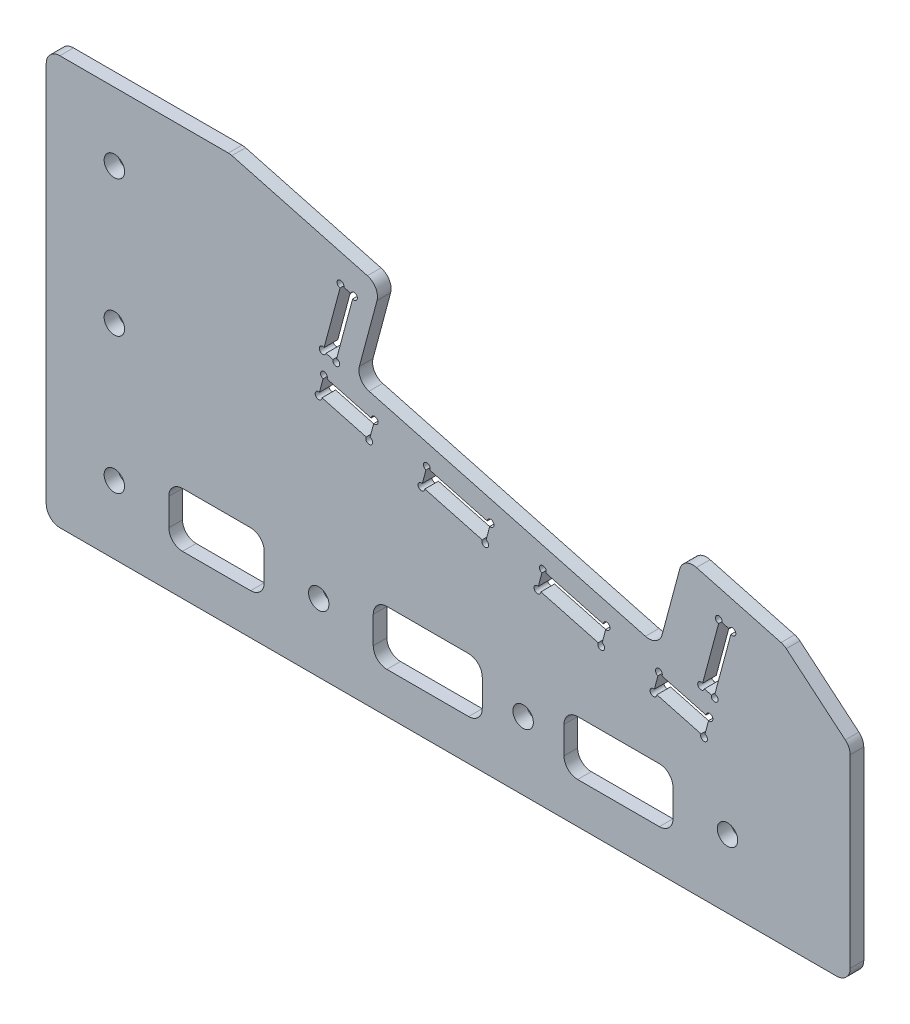
SolidWorks part; units mm, degrees
material "Thornel Mat VMA"
ref_plane "前视基准面" through (0, 0, 0) normal (0, 0, 1) x (1, 0, 0)
ref_plane "上视基准面" through (0, 0, 0) normal (0, 1, 0) x (1, 0, 0)
ref_plane "右视基准面" through (0, 0, 0) normal (1, 0, 0) x (0, 0, -1)
sketch "草图1" plane through (0, 0, 0) normal (0, 0, 1) x (1, 0, 0)
  line L1 (0, 0) -> (130, 0)
  line L2 (0, 0) -> (0, 60)
  line L3 (0, 60) -> (130, 60)
  line L4 (130, 0) -> (130, 60)
  circle A0 centre (10, 10) radius 1.5
  circle A1 centre (10, 30) radius 1.5
  circle A2 centre (10, 50) radius 1.5
  circle A3 centre (40, 10) radius 1.5
  circle A4 centre (70, 10) radius 1.5
  circle A5 centre (100, 10) radius 1.5
  dimension "D3" = 3
  dimension "D1" = 60
  dimension "D2" = 130
  dimension "D4" = 10
  dimension "D5" = 10
  dimension "D6" = 20
  dimension "D7" = 20
  dimension "D8" = 30
  dimension "D9" = 30
  dimension "D10" = 30
extrude "凸台-拉伸1" add sketch "草图1" along normal blind 2
sketch "草图2" plane through (0, 0, 2) normal (0, 0, 1) x (1, 0, 0)
  line L0 (27, 60) -> (130, 32.4012)
  line L1 (130, 60) -> (0, 60) construction
  line L2 (130, 0) -> (130, 60) construction
  line L3 (0, 60) -> (0, 0) construction
  line L4 (27, 60) -> (130, 60)
  line L5 (130, 60) -> (130, 32.4012)
  dimension "D1" = 27
  dimension "D2" = 15
extrude "切除-拉伸1" cut sketch "草图2" against normal through all
sketch "草图3" plane through (0, 0, 2) normal (0, 0, 1) x (1, 0, 0)
  line L0 (49.0714, 54.086) -> (93.504, 42.1803)
  line L1 (49.0714, 54.086) -> (45.4479, 40.563)
  line L2 (93.504, 42.1803) -> (89.8805, 28.6573)
  line L3 (45.4479, 40.563) -> (89.8805, 28.6573)
  line L4 (27, 60) -> (130, 32.4012) construction
  dimension "D1" = 14
  dimension "D2" = 46
  dimension "D3" = 22.85
extrude "切除-拉伸2" cut sketch "草图3" against normal through all
sketch "草图4" plane through (0, 0, 2) normal (0, 0, 1) x (1, 0, 0)
  line L0 (45.4479, 40.563) -> (89.8805, 28.6573) construction
  line L1 (98.7472, 36.6343) -> (96.159, 26.975)
  line L2 (96.159, 26.975) -> (98.0909, 26.4574)
  line L3 (98.0909, 26.4574) -> (100.6791, 36.1166)
  line L4 (49.0714, 54.086) -> (45.4479, 40.563) construction
  line L5 (100.6791, 36.1166) -> (98.7472, 36.6343)
  line L7 (89.8805, 28.6573) -> (93.504, 42.1803) construction
  line L8 (45.1384, 50.9987) -> (42.5502, 41.3395)
  line L9 (45.1384, 50.9987) -> (43.2065, 51.5164)
  line L10 (42.5502, 41.3395) -> (40.6183, 41.8571)
  line L11 (43.2065, 51.5164) -> (40.6183, 41.8571)
  line L13 (93.504, 42.1803) -> (130, 32.4012) construction
  dimension "D2" = 3
  dimension "D3" = 6.5
  dimension "D4" = 4
  dimension "D5" = 10
  dimension "D6" = 2
  dimension "D18" = 10
  dimension "D19" = 2
extrude "切除-拉伸5" cut sketch "草图4" against normal blind 10
sketch "草图5" plane through (0, 0, 2) normal (0, 0, 1) x (1, 0, 0)
  line L0 (108.2873, 38.2191) -> (130, 20) construction
  line L1 (93.504, 42.1803) -> (130, 32.4012) construction
  line L2 (130, 0) -> (130, 32.4012) construction
  line L3 (130, 20) -> (130, 32.4012)
  line L4 (130, 32.4012) -> (108.2873, 38.2191)
  line L5 (130, 20) -> (0, 20) construction
  line L6 (0, 60) -> (0, 0) construction
  line L7 (20, 0) -> (180, 0) construction
  line L8 (118, 30.0692) -> (118, 0)
  line L9 (118, 0) -> (130, 0)
  line L10 (130, 0) -> (130, 20)
  line L11 (108.2873, 38.2191) -> (118, 30.0692)
  dimension "D1" = 20
  dimension "D2" = 40
  dimension "D3" = 12
extrude "切除-拉伸6" cut sketch "草图5" against normal through all
fillet "圆角1" radius 2 10 edges at (0, 0, 1) (27, 60, 1) (49.0714, 54.086, 1) (45.4479, 40.563, 1) (89.8805, 28.6573, 1) (93.504, 42.1803, 1) (0, 60, 1) (118, 0, 1) (118, 30.0692, 1) (108.2873, 38.2191, 1)
sketch "草图6" plane through (0, 0, 0) normal (0, 0, -1) x (-1, 0, 0)
  line L0 (-30, 6) -> (-20, 6) construction
  line L1 (-18, 8) -> (-18, 12) construction
  line L2 (-20, 14) -> (-30, 14) construction
  line L3 (-32, 12) -> (-32, 8) construction
  line L4 (-62, 6) -> (-50, 6) construction
  line L5 (-48, 8) -> (-48, 12) construction
  line L6 (-50, 14) -> (-62, 14) construction
  line L7 (-64, 12) -> (-64, 8) construction
  line L8 (-78, 14) -> (-90, 14) construction
  line L9 (-76, 8) -> (-76, 12) construction
  line L10 (-118, 29.1366) -> (-118, 2)
  line L11 (-116, 0) -> (-2, 0)
  line L12 (0, 2) -> (0, 58)
  line L13 (-2, 60) -> (-26.7367, 60)
  line L14 (-27.2543, 59.9319) -> (-47.1396, 54.6036)
  line L15 (-48.5538, 52.1541) -> (-45.9656, 42.4949)
  line L16 (-47.3798, 40.0454) -> (-87.9487, 29.175)
  line L17 (-90.3982, 30.5892) -> (-92.9864, 40.2485)
  line L18 (-95.4358, 41.6627) -> (-107.859, 38.3339)
  line L19 (-108.6269, 37.9341) -> (-117.2856, 30.6687)
  line L20 (-118, 29.1366) -> (-118, 2)
  line L21 (-116, 0) -> (-2, 0)
  line L22 (0, 2) -> (0, 58)
  line L23 (-2, 60) -> (-26.7367, 60)
  line L24 (-27.2543, 59.9319) -> (-47.1396, 54.6036)
  line L25 (-48.5538, 52.1541) -> (-45.9656, 42.4949)
  line L26 (-47.3798, 40.0454) -> (-87.9487, 29.175)
  line L27 (-90.3982, 30.5892) -> (-92.9864, 40.2485)
  line L28 (-95.4358, 41.6627) -> (-107.859, 38.3339)
  line L29 (-108.6269, 37.9341) -> (-117.2856, 30.6687)
  line L30 (-90, 6) -> (-78, 6) construction
  line L31 (-92, 12) -> (-92, 8) construction
  line L32 (-30, 6) -> (-20, 6)
  line L33 (-18, 8) -> (-18, 12)
  line L34 (-20, 14) -> (-30, 14)
  line L35 (-32, 12) -> (-32, 8)
  line L36 (-62, 6) -> (-50, 6)
  line L37 (-48, 8) -> (-48, 12)
  line L38 (-50, 14) -> (-62, 14)
  line L39 (-64, 12) -> (-64, 8)
  line L40 (-78, 14) -> (-90, 14)
  line L41 (-76, 8) -> (-76, 12)
  line L42 (-90, 6) -> (-78, 6)
  line L43 (-92, 12) -> (-92, 8)
  arc A0 (-124, 8) -> (-122, 6) centre (-122, 8) ccw construction
  arc A1 (-124, 8) -> (-122, 6) centre (-122, 8) ccw
  arc A2 (-32, 8) -> (-30, 6) centre (-30, 8) ccw construction
  arc A3 (-20, 6) -> (-18, 8) centre (-20, 8) ccw construction
  arc A4 (-18, 12) -> (-20, 14) centre (-20, 12) ccw construction
  arc A5 (-30, 14) -> (-32, 12) centre (-30, 12) ccw construction
  arc A6 (-64, 8) -> (-62, 6) centre (-62, 8) ccw construction
  arc A7 (-50, 6) -> (-48, 8) centre (-50, 8) ccw construction
  arc A8 (-48, 12) -> (-50, 14) centre (-50, 12) ccw construction
  arc A9 (-62, 14) -> (-64, 12) centre (-62, 12) ccw construction
  arc A10 (-118, 2) -> (-116, 0) centre (-116, 2) ccw
  arc A11 (-2, 0) -> (0, 2) centre (-2, 2) ccw
  arc A12 (0, 58) -> (-2, 60) centre (-2, 58) ccw
  arc A13 (-26.7367, 60) -> (-27.2543, 59.9319) centre (-26.7367, 58) ccw
  arc A14 (-47.1396, 54.6036) -> (-48.5538, 52.1541) centre (-46.6219, 52.6718) ccw
  arc A15 (-47.3798, 40.0454) -> (-45.9656, 42.4949) centre (-47.8974, 41.9772) ccw
  arc A16 (-90.3982, 30.5892) -> (-87.9487, 29.175) centre (-88.4663, 31.1068) ccw
  arc A17 (-92.9864, 40.2485) -> (-95.4358, 41.6627) centre (-94.9182, 39.7308) ccw
  arc A18 (-107.859, 38.3339) -> (-108.6269, 37.9341) centre (-107.3414, 36.402) ccw
  arc A19 (-117.2856, 30.6687) -> (-118, 29.1366) centre (-116, 29.1366) ccw
  arc A20 (-118, 2) -> (-116, 0) centre (-116, 2) ccw
  arc A21 (-2, 0) -> (0, 2) centre (-2, 2) ccw
  arc A22 (0, 58) -> (-2, 60) centre (-2, 58) ccw
  arc A23 (-26.7367, 60) -> (-27.2543, 59.9319) centre (-26.7367, 58) ccw
  arc A24 (-47.1396, 54.6036) -> (-48.5538, 52.1541) centre (-46.6219, 52.6718) ccw
  arc A25 (-47.3798, 40.0454) -> (-45.9656, 42.4949) centre (-47.8974, 41.9772) ccw
  arc A26 (-90.3982, 30.5892) -> (-87.9487, 29.175) centre (-88.4663, 31.1068) ccw
  arc A27 (-92.9864, 40.2485) -> (-95.4358, 41.6627) centre (-94.9182, 39.7308) ccw
  arc A28 (-107.859, 38.3339) -> (-108.6269, 37.9341) centre (-107.3414, 36.402) ccw
  arc A29 (-117.2856, 30.6687) -> (-118, 29.1366) centre (-116, 29.1366) ccw
  arc A30 (-76, 12) -> (-78, 14) centre (-78, 12) ccw construction
  arc A31 (-78, 6) -> (-76, 8) centre (-78, 8) ccw construction
  arc A32 (-92, 8) -> (-90, 6) centre (-90, 8) ccw construction
  arc A33 (-90, 14) -> (-92, 12) centre (-90, 12) ccw construction
  arc A34 (-32, 8) -> (-30, 6) centre (-30, 8) ccw
  arc A35 (-20, 6) -> (-18, 8) centre (-20, 8) ccw
  arc A36 (-18, 12) -> (-20, 14) centre (-20, 12) ccw
  arc A37 (-30, 14) -> (-32, 12) centre (-30, 12) ccw
  arc A38 (-64, 8) -> (-62, 6) centre (-62, 8) ccw
  arc A39 (-50, 6) -> (-48, 8) centre (-50, 8) ccw
  arc A40 (-48, 12) -> (-50, 14) centre (-50, 12) ccw
  arc A41 (-62, 14) -> (-64, 12) centre (-62, 12) ccw
  arc A42 (-76, 12) -> (-78, 14) centre (-78, 12) ccw
  arc A43 (-78, 6) -> (-76, 8) centre (-78, 8) ccw
  arc A44 (-92, 8) -> (-90, 6) centre (-90, 8) ccw
  arc A45 (-90, 14) -> (-92, 12) centre (-90, 12) ccw
  dimension "D1" = 0
extrude "切除-拉伸7" cut sketch "草图6" against normal blind 3 contours L40 A45 L43 A44 L42 A43 L41 A42 | L38 A41 L39 A38 L36 A39 L37 A40 | L34 A37 L35 A34 L32 A35 L33 A36
sketch "草图7" plane through (0, 0, 2) normal (0, 0, 1) x (1, 0, 0)
  line L0 (98.0909, 26.4574) -> (95.0706, 15.1855) construction
  line L1 (97.3144, 23.5596) -> (89.9444, 25.5344)
  line L2 (89.9444, 25.5344) -> (89.168, 22.6366)
  line L3 (89.168, 22.6366) -> (96.538, 20.6618)
  line L4 (96.538, 20.6618) -> (97.3144, 23.5596)
  line L5 (96.159, 26.975) -> (98.0909, 26.4574) construction
  line L6 (34.4437, 37.2999) -> (89.168, 22.6366) construction
  line L7 (81.4406, 24.7072) -> (82.217, 27.6049)
  line L8 (82.217, 27.6049) -> (72.9152, 30.0974)
  line L9 (72.9152, 30.0974) -> (72.1387, 27.1996)
  line L10 (72.1387, 27.1996) -> (81.4406, 24.7072)
  line L11 (64.4113, 29.2702) -> (65.1877, 32.1679)
  line L12 (65.1877, 32.1679) -> (55.8859, 34.6604)
  line L13 (55.8859, 34.6604) -> (55.1094, 31.7626)
  line L14 (55.1094, 31.7626) -> (64.4113, 29.2702)
  line L15 (47.382, 33.8331) -> (48.1585, 36.7309)
  line L16 (48.1585, 36.7309) -> (40.7885, 38.7057)
  line L17 (40.7885, 38.7057) -> (40.012, 35.8079)
  line L18 (40.012, 35.8079) -> (47.382, 33.8331)
  dimension "D4" = 7.63
  dimension "D1" = 3
  dimension "D2" = 3
  dimension "D3" = 7.63
  dimension "D5" = 9.63
  dimension "D6" = 9.63
  dimension "D7" = 8
  dimension "D8" = 8
  dimension "D9" = 8
extrude "切除-拉伸8" cut sketch "草图7" against normal blind 10
sketch "草图8" plane through (0, 0, 2) normal (0, 0, 1) x (1, 0, 0)
  line L0 (98.726, 36.671) -> (96.1223, 26.9538)
  line L1 (96.1223, 26.9538) -> (98.1121, 26.4206)
  line L2 (98.1121, 26.4206) -> (100.7158, 36.1379)
  line L3 (100.7158, 36.1379) -> (98.726, 36.671)
  line L4 (98.7472, 36.6343) -> (96.159, 26.975)
  line L5 (100.6791, 36.1166) -> (98.7472, 36.6343)
  line L6 (98.0909, 26.4574) -> (100.6791, 36.1166)
  line L7 (96.159, 26.975) -> (98.0909, 26.4574)
  line L8 (98.7472, 36.6343) -> (96.159, 26.975)
  line L9 (100.6791, 36.1166) -> (98.7472, 36.6343)
  line L10 (98.0909, 26.4574) -> (100.6791, 36.1166)
  line L11 (96.159, 26.975) -> (98.0909, 26.4574)
  line L12 (97.3144, 23.5596) -> (89.9444, 25.5344)
  line L13 (96.538, 20.6618) -> (97.3144, 23.5596)
  line L14 (89.168, 22.6366) -> (96.538, 20.6618)
  line L15 (89.9444, 25.5344) -> (89.168, 22.6366)
  line L16 (97.3144, 23.5596) -> (89.9444, 25.5344)
  line L17 (96.538, 20.6618) -> (97.3144, 23.5596)
  line L18 (89.168, 22.6366) -> (96.538, 20.6618)
  line L19 (89.9444, 25.5344) -> (89.168, 22.6366)
  line L20 (81.4406, 24.7072) -> (82.217, 27.6049)
  line L21 (72.1387, 27.1996) -> (81.4406, 24.7072)
  line L22 (72.9152, 30.0974) -> (72.1387, 27.1996)
  line L23 (82.217, 27.6049) -> (72.9152, 30.0974)
  line L24 (81.4406, 24.7072) -> (82.217, 27.6049)
  line L25 (72.1387, 27.1996) -> (81.4406, 24.7072)
  line L26 (72.9152, 30.0974) -> (72.1387, 27.1996)
  line L27 (82.217, 27.6049) -> (72.9152, 30.0974)
  line L28 (64.4113, 29.2702) -> (65.1877, 32.1679)
  line L29 (55.1094, 31.7626) -> (64.4113, 29.2702)
  line L30 (55.8859, 34.6604) -> (55.1094, 31.7626)
  line L31 (65.1877, 32.1679) -> (55.8859, 34.6604)
  line L32 (64.4113, 29.2702) -> (65.1877, 32.1679)
  line L33 (55.1094, 31.7626) -> (64.4113, 29.2702)
  line L34 (55.8859, 34.6604) -> (55.1094, 31.7626)
  line L35 (65.1877, 32.1679) -> (55.8859, 34.6604)
  line L36 (47.382, 33.8331) -> (48.1585, 36.7309)
  line L37 (40.012, 35.8079) -> (47.382, 33.8331)
  line L38 (40.7885, 38.7057) -> (40.012, 35.8079)
  line L39 (48.1585, 36.7309) -> (40.7885, 38.7057)
  line L40 (47.382, 33.8331) -> (48.1585, 36.7309)
  line L41 (40.012, 35.8079) -> (47.382, 33.8331)
  line L42 (40.7885, 38.7057) -> (40.012, 35.8079)
  line L43 (48.1585, 36.7309) -> (40.7885, 38.7057)
  line L44 (43.2065, 51.5164) -> (40.6183, 41.8571)
  line L45 (45.1384, 50.9987) -> (43.2065, 51.5164)
  line L46 (42.5502, 41.3395) -> (45.1384, 50.9987)
  line L47 (40.6183, 41.8571) -> (42.5502, 41.3395)
  line L48 (43.2065, 51.5164) -> (40.6183, 41.8571)
  line L49 (45.1384, 50.9987) -> (43.2065, 51.5164)
  line L50 (42.5502, 41.3395) -> (45.1384, 50.9987)
  line L51 (40.6183, 41.8571) -> (42.5502, 41.3395)
  line L52 (97.3512, 23.5808) -> (89.9232, 25.5711)
  line L53 (89.9232, 25.5711) -> (89.1312, 22.6154)
  line L54 (89.1312, 22.6154) -> (96.5592, 20.6251)
  line L55 (96.5592, 20.6251) -> (97.3512, 23.5808)
  line L56 (81.4618, 24.6704) -> (82.2538, 27.6262)
  line L57 (82.2538, 27.6262) -> (72.8939, 30.1341)
  line L58 (72.8939, 30.1341) -> (72.102, 27.1784)
  line L59 (72.102, 27.1784) -> (81.4618, 24.6704)
  line L60 (64.4325, 29.2334) -> (65.2245, 32.1891)
  line L61 (65.2245, 32.1891) -> (55.8647, 34.6971)
  line L62 (55.8647, 34.6971) -> (55.0727, 31.7414)
  line L63 (55.0727, 31.7414) -> (64.4325, 29.2334)
  line L64 (47.4032, 33.7964) -> (48.1952, 36.7521)
  line L65 (48.1952, 36.7521) -> (40.7672, 38.7424)
  line L66 (40.7672, 38.7424) -> (39.9753, 35.7867)
  line L67 (39.9753, 35.7867) -> (47.4032, 33.7964)
  line L68 (43.1853, 51.5531) -> (40.5816, 41.8359)
  line L69 (40.5816, 41.8359) -> (42.5714, 41.3027)
  line L70 (42.5714, 41.3027) -> (45.1751, 51.02)
  line L71 (45.1751, 51.02) -> (43.1853, 51.5531)
  dimension "D1" = 0
  dimension "D2" = 0
  dimension "D3" = 0
  dimension "D4" = 0
  dimension "D5" = 0
  dimension "D6" = 0
  dimension "D7" = 0.03
extrude "切除-拉伸9" cut sketch "草图8" against normal blind 10 contours L60 L61 L62 L63 | L64 L65 L66 L67 | L68 L69 L70 L71 | L0 L1 L2 L3 | L52 L53 L54 L55 | L56 L57 L58 L59
sketch "草图9" plane through (0, 0, 2) normal (0, 0, 1) x (1, 0, 0)
  circle A0 centre (43.1853, 51.5531) radius 0.5
  circle A1 centre (45.1751, 51.02) radius 0.5
  circle A2 centre (40.5816, 41.8359) radius 0.5
  circle A3 centre (42.5714, 41.3027) radius 0.5
  circle A4 centre (40.7672, 38.7424) radius 0.5
  circle A5 centre (48.1952, 36.7521) radius 0.5
  circle A6 centre (39.9753, 35.7867) radius 0.5
  circle A7 centre (47.4032, 33.7964) radius 0.5
  circle A8 centre (55.8647, 34.6971) radius 0.5
  circle A9 centre (55.0727, 31.7414) radius 0.5
  circle A10 centre (65.2245, 32.1891) radius 0.5
  circle A11 centre (64.4325, 29.2334) radius 0.5
  circle A12 centre (72.102, 27.1784) radius 0.5
  circle A13 centre (72.8939, 30.1341) radius 0.5
  circle A14 centre (82.2538, 27.6262) radius 0.5
  circle A15 centre (81.4618, 24.6704) radius 0.5
  circle A16 centre (89.1312, 22.6154) radius 0.5
  circle A17 centre (89.9232, 25.5711) radius 0.5
  circle A18 centre (97.3512, 23.5808) radius 0.5
  circle A19 centre (96.5592, 20.6251) radius 0.5
  circle A20 centre (96.1223, 26.9538) radius 0.5
  circle A21 centre (98.1121, 26.4206) radius 0.5
  circle A22 centre (98.726, 36.671) radius 0.5
  circle A23 centre (100.7158, 36.1379) radius 0.5
  dimension "D1" = 1
sketch "草图10" plane through (0, 0, 2) normal (0, 0, 1) x (1, 0, 0)
  line L0 (40.7672, 38.7424) -> (48.1952, 36.7521)
  line L1 (40.7672, 38.7424) -> (40.7414, 38.6458)
  line L2 (48.1952, 36.7521) -> (48.1693, 36.6555)
  line L3 (40.7414, 38.6458) -> (48.1693, 36.6555)
  line L4 (39.9753, 35.7867) -> (47.4032, 33.7964)
  line L5 (39.9753, 35.7867) -> (40.0011, 35.8833)
  line L6 (47.4032, 33.7964) -> (47.4291, 33.893)
  line L7 (40.0011, 35.8833) -> (47.4291, 33.893)
  line L8 (55.8647, 34.6971) -> (55.8388, 34.6005)
  line L9 (55.8647, 34.6971) -> (65.2229, 32.1896)
  line L10 (55.8388, 34.6005) -> (65.197, 32.093)
  line L11 (65.2229, 32.1896) -> (65.197, 32.093)
  line L12 (55.8647, 34.6971) -> (55.0727, 31.7414) construction
  line L14 (64.4325, 29.2334) -> (55.0727, 31.7414)
  line L15 (64.4325, 29.2334) -> (64.4584, 29.33)
  line L16 (55.0727, 31.7414) -> (55.0986, 31.838)
  line L17 (64.4584, 29.33) -> (55.0986, 31.838)
  line L18 (72.8939, 30.1341) -> (82.2538, 27.6262)
  line L19 (72.8939, 30.1341) -> (72.8681, 30.0375)
  line L20 (82.2538, 27.6262) -> (82.2279, 27.5296)
  line L21 (72.8681, 30.0375) -> (82.2279, 27.5296)
  line L22 (81.4618, 24.6704) -> (72.102, 27.1784)
  line L23 (81.4618, 24.6704) -> (81.4877, 24.767)
  line L24 (72.102, 27.1784) -> (72.1278, 27.275)
  line L25 (81.4877, 24.767) -> (72.1278, 27.275)
  line L26 (89.9232, 25.5711) -> (97.3512, 23.5808)
  line L27 (89.9232, 25.5711) -> (89.8973, 25.4745)
  line L28 (97.3512, 23.5808) -> (97.3253, 23.4842)
  line L29 (89.8973, 25.4745) -> (97.3253, 23.4842)
  line L30 (96.5592, 20.6251) -> (89.1312, 22.6154)
  line L31 (96.5592, 20.6251) -> (96.5851, 20.7217)
  line L32 (89.1312, 22.6154) -> (89.1571, 22.712)
  line L33 (96.5851, 20.7217) -> (89.1571, 22.712)
  line L34 (98.726, 36.671) -> (96.1223, 26.9538)
  line L35 (98.726, 36.671) -> (98.8226, 36.6451)
  line L36 (96.1223, 26.9538) -> (96.2189, 26.9279)
  line L37 (98.8226, 36.6451) -> (96.2189, 26.9279)
  line L38 (100.7158, 36.1379) -> (98.1121, 26.4206)
  line L39 (100.7158, 36.1379) -> (100.6192, 36.1637)
  line L40 (98.1121, 26.4206) -> (98.0155, 26.4465)
  line L41 (100.6192, 36.1637) -> (98.0155, 26.4465)
  line L42 (43.1853, 51.5531) -> (40.5816, 41.8359)
  line L43 (43.1853, 51.5531) -> (43.2626, 51.5324)
  line L44 (40.5816, 41.8359) -> (40.6588, 41.8152)
  line L45 (43.2626, 51.5324) -> (40.6588, 41.8152)
  line L46 (45.1751, 51.02) -> (42.5714, 41.3027)
  line L47 (45.1751, 51.02) -> (45.0978, 51.0407)
  line L48 (42.5714, 41.3027) -> (42.4941, 41.3234)
  line L49 (45.0978, 51.0407) -> (42.4941, 41.3234)
  dimension "D1" = 0.08
  dimension "D2" = 0.08
  dimension "D3" = 0.1
  dimension "D4" = 0.1
  dimension "D5" = 0.1
  dimension "D6" = 0.1
  dimension "D7" = 0.1
  dimension "D8" = 0.1
  dimension "D9" = 0.1
  dimension "D10" = 0.1
  dimension "D11" = 0.1
  dimension "D12" = 0.1
extrude "凸台-拉伸2" add sketch "草图10" against normal up to surface (2 mm away) up to face at (44.0852, 36.2694, 0)
extrude "切除-拉伸10" cut sketch "草图9" against normal blind 10
